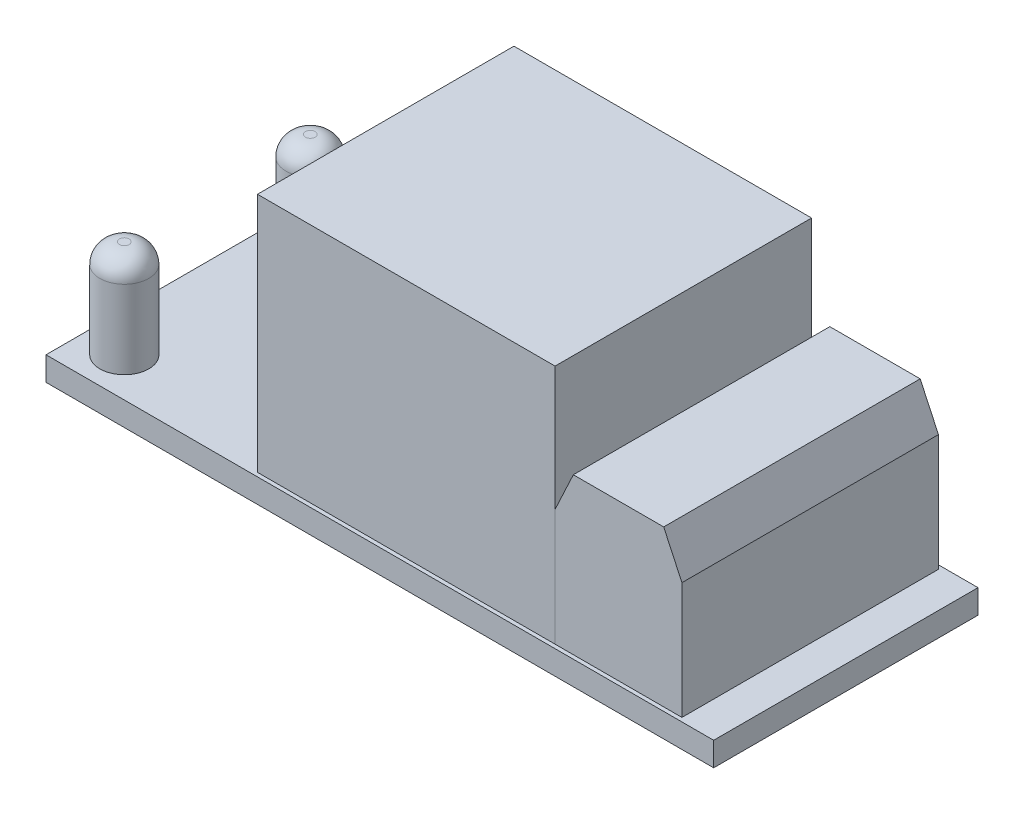
SolidWorks part; units mm, degrees
ref_plane "Front Plane" through (0, 0, 0) normal (0, 0, 1) x (1, 0, 0)
ref_plane "Top Plane" through (0, 0, 0) normal (0, 1, 0) x (1, 0, 0)
ref_plane "Right Plane" through (0, 0, 0) normal (1, 0, 0) x (0, 0, -1)
sketch "Sketch1" plane through (0, 0, 0) normal (0, 1, 0) x (1, 0, 0)
  line L1 (21.6535, -8.5725) -> (-21.6535, -8.5725)
  line L2 (21.6535, -8.5725) -> (21.6535, 8.5725)
  line L3 (21.6535, 8.5725) -> (-21.6535, 8.5725)
  line L4 (-21.6535, -8.5725) -> (-21.6535, 8.5725)
  line L5 (21.6535, -8.5725) -> (-21.6535, 8.5725) construction
  line L6 (21.6535, 8.5725) -> (-21.6535, -8.5725) construction
  point P0 (0, 0)
  dimension "D1" = 17.145
  dimension "D2" = 43.307
extrude "Boss-Extrude1" add sketch "Sketch1" along normal blind 1.5494
sketch "Sketch2" plane through (0, 1.5494, 0) normal (0, 1, 0) x (1, 0, 0)
  line L0 (-21.6535, -8.5725) -> (21.6535, -8.5725) construction
  line L1 (-8.1915, 8.3185) -> (11.1125, 8.3185)
  line L2 (-8.1915, 8.3185) -> (-8.1915, -8.3185)
  line L3 (-8.1915, -8.3185) -> (11.1125, -8.3185)
  line L4 (11.1125, 8.3185) -> (11.1125, -8.3185)
  line L5 (21.6535, 8.5725) -> (-21.6535, 8.5725) construction
  line L6 (21.6535, -8.5725) -> (21.6535, 8.5725) construction
  line L7 (-21.6535, 8.5725) -> (-21.6535, -8.5725) construction
  dimension "D1" = 0.254
  dimension "D2" = 0.254
  dimension "D3" = 10.541
  dimension "D4" = 13.462
extrude "Boss-Extrude2" add sketch "Sketch2" along normal blind 15.621
sketch "Sketch3" plane through (0, 1.5494, 0) normal (0, 1, 0) x (1, 0, 0)
  line L0 (21.6535, 8.5725) -> (-21.6535, 8.5725) construction
  line L1 (11.1125, -8.3185) -> (19.3421, -8.3185)
  line L2 (11.1125, -8.3185) -> (11.1125, 8.3185)
  line L3 (11.1125, 8.3185) -> (19.3421, 8.3185)
  line L4 (19.3421, -8.3185) -> (19.3421, 8.3185)
  dimension "D1" = 0.254
  dimension "D2" = 8.2296
extrude "Boss-Extrude3" add sketch "Sketch3" along normal blind 10.1092 separate body
chamfer "Chamfer1" distance 2.54 angle 25 2 edges at (19.3421, 11.6586, 0) (11.1125, 11.6586, 0)
sketch "Sketch4" plane through (0, 1.5494, 0) normal (0, 1, 0) x (1, 0, 0)
  line L0 (-21.6535, 8.5725) -> (-21.6535, -8.5725) construction
  line L1 (21.6535, 8.5725) -> (-21.6535, 8.5725) construction
  line L2 (-21.6535, -8.5725) -> (21.6535, -8.5725) construction
  circle A0 centre (-19.1135, -6.0325) radius 1.5875
  circle A1 centre (-19.1135, 6.0325) radius 1.5875
  point P8 (0, 0)
  dimension "D1" = 3.175
  dimension "D2" = 3.175
  dimension "D3" = 2.54
  dimension "D4" = 2.54
  dimension "D5" = 2.54
  dimension "D6" = 2.54
extrude "Boss-Extrude4" add sketch "Sketch4" along normal blind 6.35 separate body contours A1
fillet "Fillet2" radius 1.27 1 edges at (-19.1135, 7.8994, -4.445)
sketch "Sketch5" plane through (0, 1.5494, 0) normal (0, 1, 0) x (1, 0, 0)
  circle A0 centre (-19.1135, -6.0325) radius 1.5875 construction
  circle A1 centre (-19.1135, -6.0325) radius 1.5875
extrude "Boss-Extrude5" add sketch "Sketch5" along normal blind 6.35
fillet "Fillet1" radius 1.27 1 edges at (-19.1135, 7.8994, 7.62)
